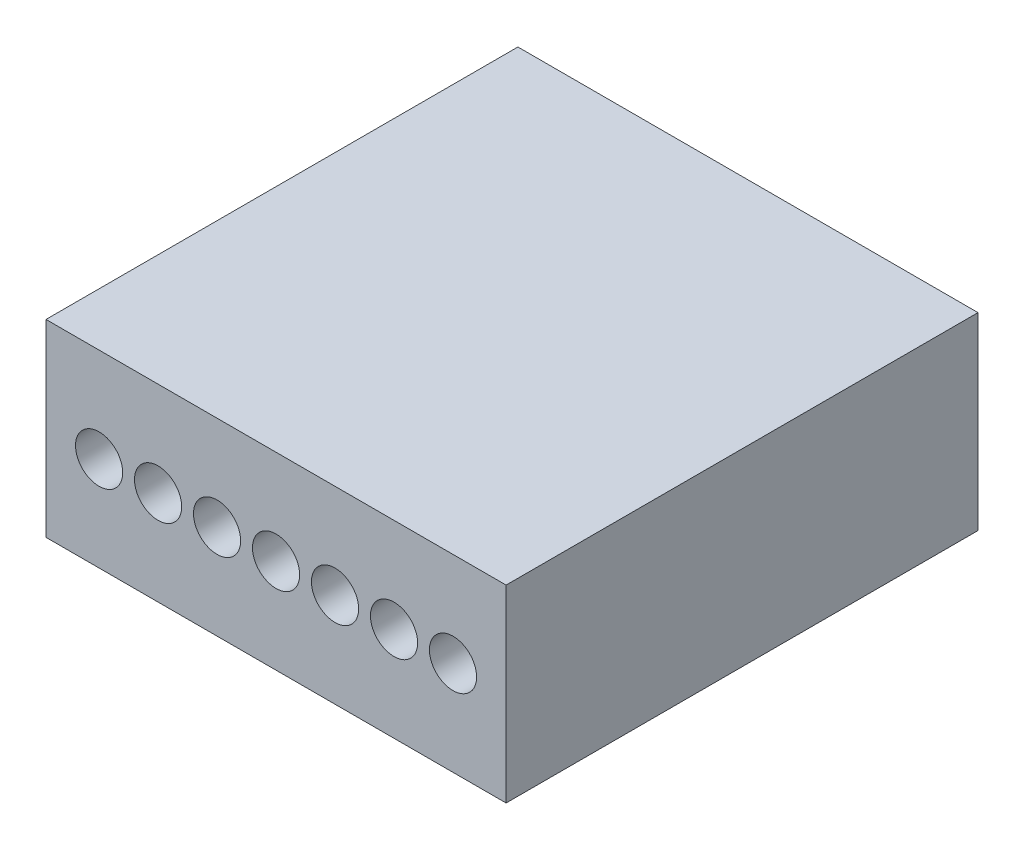
SolidWorks part; units mm, degrees
ref_plane "Front Plane" through (0, 0, 0) normal (0, 0, 1) x (1, 0, 0)
ref_plane "Top Plane" through (0, 0, 0) normal (0, 1, 0) x (1, 0, 0)
ref_plane "Right Plane" through (0, 0, 0) normal (1, 0, 0) x (0, 0, -1)
sketch "Sketch2" plane through (0, 0, 0) normal (0, 0, 1) x (1, 0, 0)
  line L1 (0, 0) -> (9.75, 0)
  line L2 (0, 0) -> (0, 4)
  line L3 (0, 4) -> (9.75, 4)
  line L4 (9.75, 0) -> (9.75, 4)
  dimension "D1" = 9.75
  dimension "D2" = 4
extrude "Boss-Extrude1" add sketch "Sketch2" along normal blind 10
sketch "Sketch3" plane through (0, 0, 10) normal (0, 0, 1) x (1, 0, 0)
  line L0 (0, 2) -> (9.75, 2) construction
  line L1 (0, 4) -> (0, 0) construction
  line L2 (9.75, 0) -> (9.75, 4) construction
  line L3 (0, 2) -> (9.75, 2) construction
  line L4 (9.75, 4) -> (0, 4) construction
  line L5 (0, 0) -> (9.75, 0) construction
  line L6 (1.125, 4) -> (1.125, 0) construction
  circle A0 centre (1.125, 2) radius 0.5
  circle A1 centre (2.375, 2) radius 0.5
  circle A2 centre (3.625, 2) radius 0.5
  circle A3 centre (4.875, 2) radius 0.5
  circle A4 centre (6.125, 2) radius 0.5
  circle A5 centre (7.375, 2) radius 0.5
  circle A6 centre (8.625, 2) radius 0.5
  circle A21 centre (24.875, 2) radius 0.5 [skipped]
  circle A22 centre (23.625, 2) radius 0.5 [skipped]
  circle A23 centre (22.375, 2) radius 0.5 [skipped]
  circle A24 centre (21.125, 2) radius 0.5 [skipped]
  circle A25 centre (19.875, 2) radius 0.5 [skipped]
  circle A26 centre (18.625, 2) radius 0.5 [skipped]
  circle A27 centre (17.375, 2) radius 0.5 [skipped]
  circle A28 centre (16.125, 2) radius 0.5 [skipped]
  circle A29 centre (14.875, 2) radius 0.5 [skipped]
  circle A30 centre (13.625, 2) radius 0.5 [skipped]
  circle A31 centre (12.375, 2) radius 0.5 [skipped]
  circle A32 centre (11.125, 2) radius 0.5 [skipped]
  circle A33 centre (9.875, 2) radius 0.5 [skipped]
  dimension "D1" = 1
  dimension "D2" = 2
  dimension "D3" = 1.125
  dimension "D5" = 1.25
  dimension "D4" = 20
extrude "Cut-Extrude1" cut sketch "Sketch3" against normal blind 5
sketch "Sketch4" plane through (0, 0, 10) normal (0, 0, 1) x (1, 0, 0)
  point P0 (1.125, 2)
  point P1 (2.375, 2)
  point P3 (3.625, 2)
  point P5 (4.875, 2)
  point P7 (6.125, 2)
  point P9 (7.375, 2)
  point P11 (8.625, 2)
  point P15 (0, 0)
  point P17 (0, 0)
  point P27 (0, 0)
  point P37 (0, 0)
